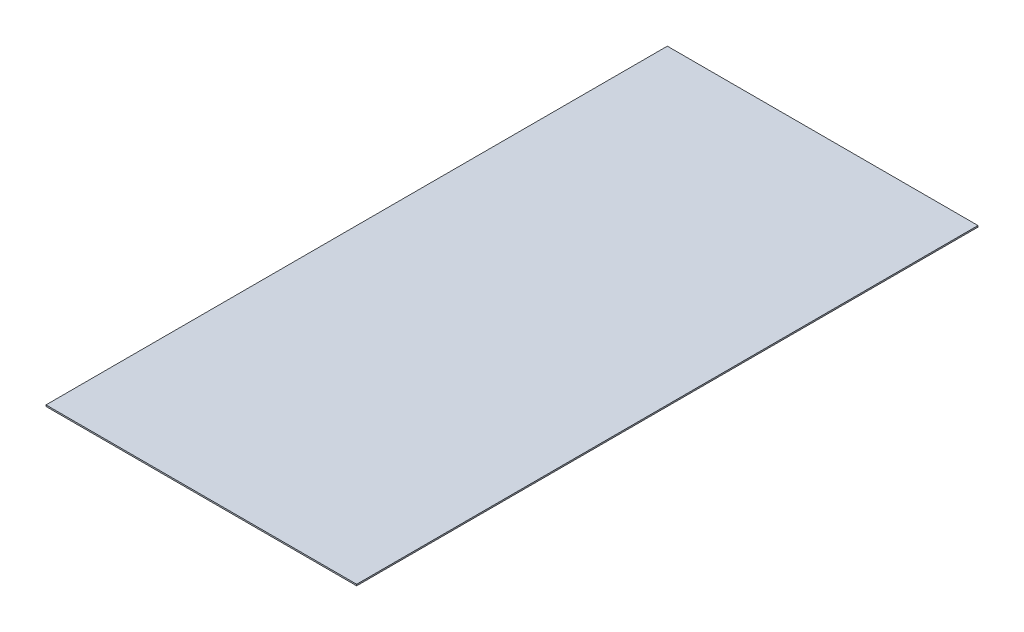
SolidWorks part; units mm, degrees
material "Teak"
ref_plane "Front Plane" through (0, 0, 0) normal (0, 0, 1) x (1, 0, 0)
ref_plane "Top Plane" through (0, 0, 0) normal (0, 1, 0) x (1, 0, 0)
ref_plane "Right Plane" through (0, 0, 0) normal (1, 0, 0) x (0, 0, -1)
sketch "Sketch1" plane through (0, 0, 0) normal (0, 1, 0) x (1, 0, 0)
  line L1 (-609.6, -1219.2) -> (609.6, -1219.2)
  line L2 (-609.6, -1219.2) -> (-609.6, 1219.2)
  line L3 (-609.6, 1219.2) -> (609.6, 1219.2)
  line L4 (609.6, -1219.2) -> (609.6, 1219.2)
  line L5 (-609.6, -1219.2) -> (609.6, 1219.2) construction
  line L6 (-609.6, 1219.2) -> (609.6, -1219.2) construction
  point P0 (0, 0)
  dimension "D1" = 1219.2
  dimension "D2" = 2438.4
extrude "Boss-Extrude1" add sketch "Sketch1" along normal blind 5.5562
